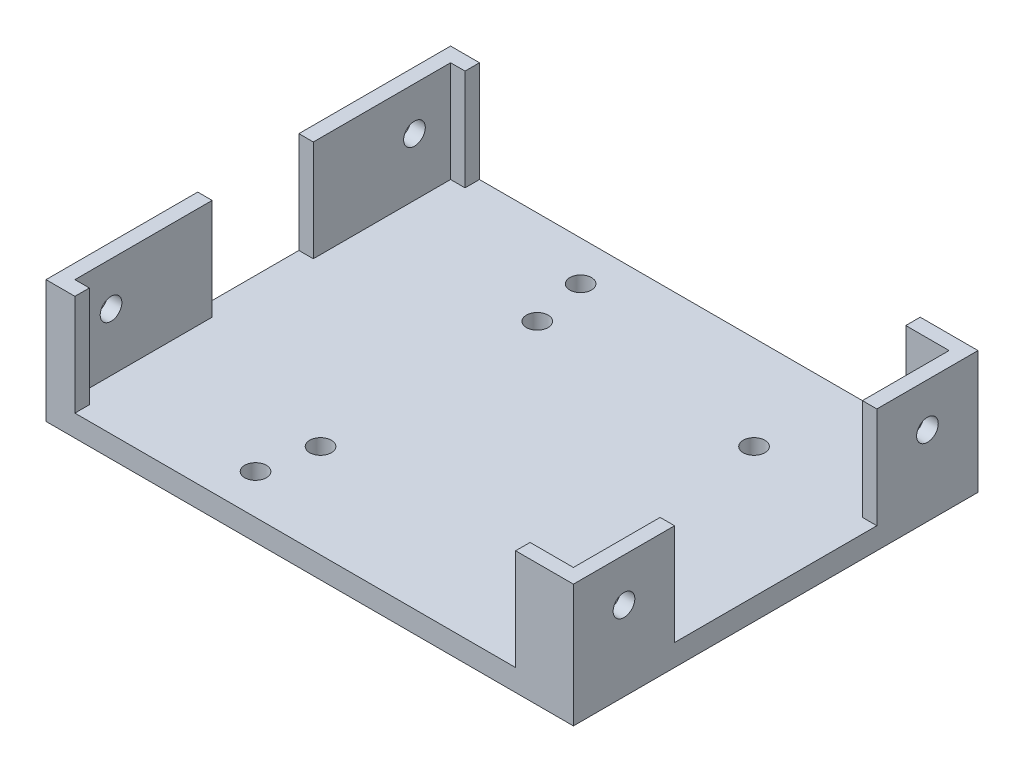
SolidWorks part; units mm, degrees
ref_plane "Front Plane" through (0, 0, 0) normal (0, 0, 1) x (1, 0, 0)
ref_plane "Top Plane" through (0, 0, 0) normal (0, 1, 0) x (1, 0, 0)
ref_plane "Right Plane" through (0, 0, 0) normal (1, 0, 0) x (0, 0, -1)
sketch "Sketch1" plane through (0, 0, 0) normal (0, 1, 0) x (1, 0, 0)
  line L1 (-37.6205, 21.9093) -> (35.3795, 21.9093)
  line L2 (-37.6205, 21.9093) -> (-37.6205, -34.0907)
  line L3 (-37.6205, -34.0907) -> (35.3795, -34.0907)
  line L4 (35.3795, 21.9093) -> (35.3795, -34.0907)
  dimension "D1" = 73
  dimension "D2" = 56
extrude "Boss-Extrude1" add sketch "Sketch1" along normal blind 3
sketch "Sketch2" plane through (0, 3, 0) normal (0, 1, 0) x (1, 0, 0)
  line L0 (35.3795, -34.0907) -> (35.3795, 21.9093) construction
  line L1 (35.3795, 21.9093) -> (-37.6205, 21.9093) construction
  line L2 (-37.6205, -34.0907) -> (35.3795, -34.0907) construction
  circle A0 centre (-12.6205, 8.9093) radius 1.5
  circle A1 centre (-12.6205, -21.0907) radius 1.5
  circle A2 centre (17.3795, -21.0907) radius 1.5
  circle A3 centre (17.3795, 8.9093) radius 1.5
  point P14 (0, 0)
  point P15 (0, 0)
  point P16 (0, 0)
  point P17 (0, 0)
  point P18 (0, 0)
  dimension "D1" = 3
  dimension "D2" = 3
  dimension "D3" = 3
  dimension "D4" = 3
  dimension "D5" = 18
  dimension "D6" = 13
  dimension "D7" = 18
  dimension "D8" = 13
  dimension "D9" = 30
  dimension "D10" = 30
  dimension "D11" = 13
  dimension "D12" = 13
extrude "Cut-Extrude1" cut sketch "Sketch2" against normal through all
sketch "Sketch3" plane through (0, 0, 0) normal (0, -1, 0) x (-1, 0, 0)
sketch "Sketch4" plane through (0, 3, 0) normal (0, 1, 0) x (1, 0, 0)
  line L0 (35.3795, 21.9093) -> (-37.6205, 21.9093) construction
  line L1 (-37.6205, 21.9093) -> (-33.6205, 21.9093)
  line L2 (-37.6205, 21.9093) -> (-37.6205, 19.9093)
  line L3 (-37.6205, 19.9093) -> (-33.6205, 19.9093)
  line L4 (-33.6205, 21.9093) -> (-33.6205, 19.9093)
  line L5 (27.3795, 21.9093) -> (35.3795, 21.9093)
  line L6 (27.3795, 21.9093) -> (27.3795, 19.9093)
  line L7 (27.3795, 19.9093) -> (35.3795, 19.9093)
  line L8 (35.3795, 21.9093) -> (35.3795, 19.9093)
  line L9 (33.3795, 19.9093) -> (35.3795, 19.9093)
  line L10 (33.3795, 19.9093) -> (33.3795, 7.9093)
  line L11 (33.3795, 7.9093) -> (35.3795, 7.9093)
  line L12 (35.3795, 19.9093) -> (35.3795, 7.9093)
  line L13 (33.3795, -20.0907) -> (35.3795, -20.0907)
  line L14 (33.3795, -20.0907) -> (33.3795, -32.0907)
  line L15 (33.3795, -32.0907) -> (35.3795, -32.0907)
  line L16 (35.3795, -20.0907) -> (35.3795, -32.0907)
  line L17 (27.3795, -32.0907) -> (35.3795, -32.0907)
  line L18 (27.3795, -32.0907) -> (27.3795, -34.0907)
  line L19 (27.3795, -34.0907) -> (35.3795, -34.0907)
  line L20 (35.3795, -32.0907) -> (35.3795, -34.0907)
  line L21 (-37.6205, -32.0907) -> (-33.6205, -32.0907)
  line L22 (-37.6205, -32.0907) -> (-37.6205, -34.0907)
  line L23 (-37.6205, -34.0907) -> (-33.6205, -34.0907)
  line L24 (-33.6205, -32.0907) -> (-33.6205, -34.0907)
  line L25 (-37.6205, 19.9093) -> (-35.6205, 19.9093)
  line L26 (-37.6205, 19.9093) -> (-37.6205, 0.9093)
  line L27 (-37.6205, 0.9093) -> (-35.6205, 0.9093)
  line L28 (-35.6205, 19.9093) -> (-35.6205, 0.9093)
  line L29 (-37.6205, -13.0907) -> (-35.6205, -13.0907)
  line L30 (-37.6205, -13.0907) -> (-37.6205, -32.0907)
  line L31 (-37.6205, -32.0907) -> (-35.6205, -32.0907)
  line L32 (-35.6205, -13.0907) -> (-35.6205, -32.0907)
  line L33 (-37.6205, 21.9093) -> (-37.6205, -34.0907) construction
  line L34 (35.3795, -34.0907) -> (35.3795, 21.9093) construction
  line L35 (-37.6205, -34.0907) -> (35.3795, -34.0907) construction
  line M36 (-37.6205, 21.9093) -> (-37.6205, -34.0907)
  line M37 (-37.6205, -34.0907) -> (35.3795, -34.0907)
  line M38 (35.3795, -34.0907) -> (35.3795, 21.9093)
  line M39 (35.3795, 21.9093) -> (-37.6205, 21.9093)
  dimension "D1" = 4
  dimension "D2" = 2
  dimension "D3" = 0
  dimension "D4" = 0
  dimension "D5" = 8
  dimension "D6" = 2
  dimension "D7" = 0
  dimension "D8" = 0
  dimension "D9" = 12
  dimension "D10" = 0
  dimension "D11" = 0
  dimension "D12" = 0
  dimension "D13" = 2
  dimension "D14" = 2
  dimension "D15" = 12
  dimension "D16" = 2
  dimension "D17" = 0
  dimension "D18" = 8
  dimension "D19" = 2
  dimension "D20" = 0
  dimension "D21" = 4
  dimension "D22" = 2
  dimension "D23" = 0
  dimension "D24" = 0
  dimension "D25" = 19
  dimension "D26" = 2
  dimension "D27" = 19
  dimension "D28" = 2
  dimension "D29" = 0
  dimension "D30" = 0
  dimension "D31" = 0
  dimension "D32" = 0
extrude "Boss-Extrude2" add sketch "Sketch4" along normal blind 14 contours L4 L3 M39 M36 | L6 L7 M38 M39 | L10 L11 L7 M38 | L14 L15 L13 M38 | L24 L21 M36 M37 | L32 L29 L21 M36 | L26 L27 L28 L25 | L17 L20 L19 L18
sketch "Sketch5" plane through (0, 3, 0) normal (0, 1, 0) x (1, 0, 0)
  line L0 (27.3795, 19.9093) -> (33.3795, 19.9093) construction
  line L1 (33.3795, -20.0907) -> (33.3795, -32.0907) construction
  line L2 (-35.6205, -32.0907) -> (-33.6205, -32.0907) construction
  circle A0 centre (30.8795, 16.4093) radius 1.5
  circle A1 centre (30.8795, -28.5907) radius 1.5
  circle A2 centre (-14.1205, 16.4093) radius 1.5
  circle A3 centre (-14.1205, -28.5907) radius 1.5
  dimension "D1" = 3
  dimension "D2" = 3
  dimension "D3" = 3
  dimension "D4" = 3
  dimension "D5" = 45
  dimension "D6" = 2.5
  dimension "D7" = 3.5
  dimension "D8" = 2.5
  dimension "D9" = 45
  dimension "D10" = 45
  dimension "D11" = 45
  dimension "D12" = 3.5
extrude "Cut-Extrude2" cut sketch "Sketch5" against normal through all
sketch "Sketch7" plane through (35.3795, 0, 0) normal (1, 0, 0) x (0, 0, -1)
  line L0 (-34.0907, 17) -> (-34.0907, 0) construction
  line L1 (-34.0907, 17) -> (-20.0907, 17) construction
  line L3 (7.9093, 17) -> (21.9093, 17) construction
  line L4 (21.9093, 17) -> (21.9093, 0) construction
  circle A0 centre (-27.0907, 11) radius 1.5
  circle A1 centre (14.9093, 11) radius 1.5
  dimension "D1" = 3
  dimension "D2" = 3
  dimension "D3" = 7
  dimension "D4" = 6
  dimension "D5" = 6
  dimension "D6" = 7
extrude "Cut-Extrude4" cut sketch "Sketch7" against normal through all both and the other way through all
